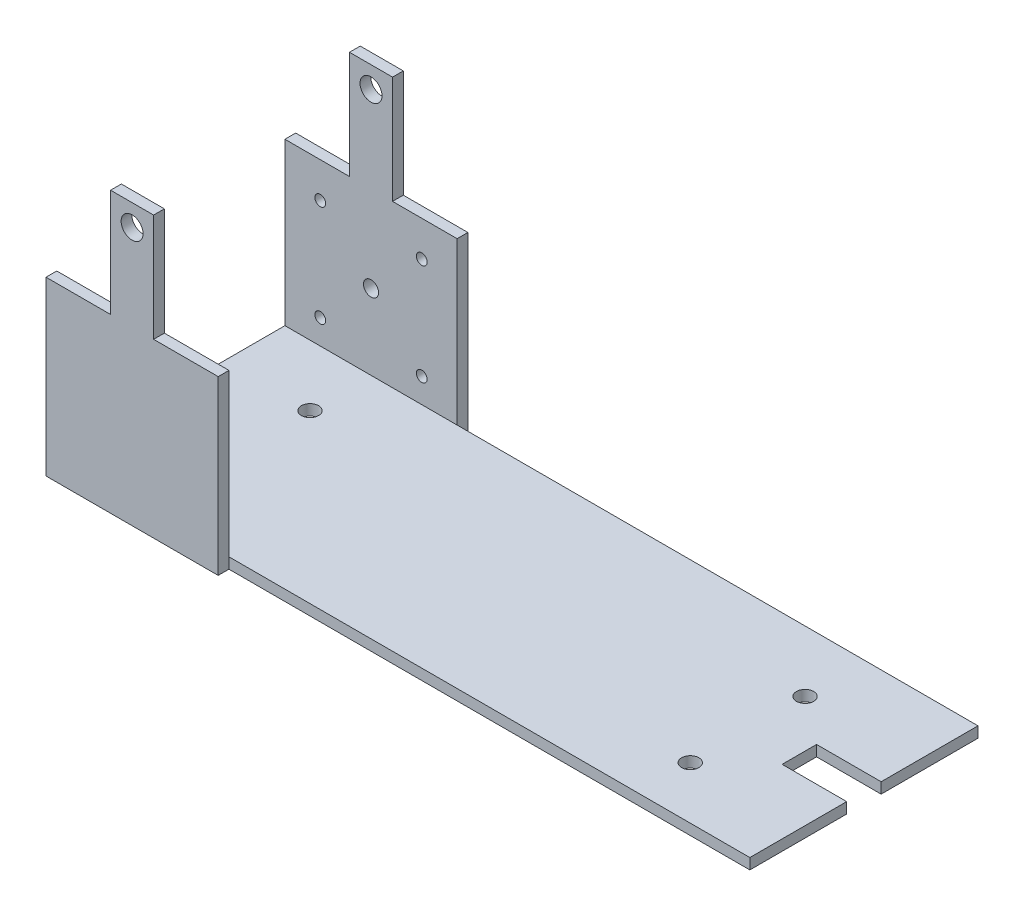
SolidWorks part; units mm, degrees
ref_plane "Front Plane" through (0, 0, 0) normal (0, 0, 1) x (1, 0, 0)
ref_plane "Top Plane" through (0, 0, 0) normal (0, 1, 0) x (1, 0, 0)
ref_plane "Right Plane" through (0, 0, 0) normal (1, 0, 0) x (0, 0, -1)
sketch "Sketch1" plane through (0, 0, 0) normal (0, 0, 1) x (1, 0, 0)
  line L0 (-40, -40) -> (-10, -40)
  line L2 (-10, -40) -> (-10, 10)
  line L3 (-10, 10) -> (10, 10)
  line L4 (10, -40) -> (10, 10)
  line L7 (40, -40) -> (40, -120)
  line L8 (40, -120) -> (-40, -120)
  line L9 (-40, -120) -> (-40, -40)
  line L10 (10, -40) -> (40, -40)
  circle A0 centre (0, 0) radius 5.1
  circle A1 centre (0, -80) radius 3.5
  dimension "D3" = 10.2
  dimension "D5" = 7
  dimension "D1" = 20
  dimension "D2" = 50
  dimension "D4" = 10
  dimension "D6" = 80
  dimension "D7" = 30
  dimension "D8" = 30
  dimension "D9" = 80
  dimension "D10" = 10
  dimension "D11" = 40
extrude "Boss-Extrude2" add sketch "Sketch1" along normal blind 5
sketch "Sketch2" plane through (0, 0, 5) normal (0, 0, 1) x (1, 0, 0)
  circle A0 centre (-23.57, -56.43) radius 2.5
  circle A1 centre (23.57, -56.43) radius 2.5
  circle A2 centre (-23.57, -103.57) radius 2.5
  circle A3 centre (23.57, -103.57) radius 2.5
extrude "Cut-Extrude1" cut sketch "Sketch2" against normal blind 10
sketch "Sketch3" plane through (0, 0, 5) normal (0, 0, 1) x (1, 0, 0)
  line L2 (-40, -120) -> (-40, -115)
  line L5 (-40, -115) -> (282, -115)
  line L6 (282, -115) -> (282, -120)
  line L7 (282, -120) -> (-40, -120)
  dimension "D1" = 5
  dimension "D2" = 322
extrude "Boss-Extrude3" add sketch "Sketch3" along normal blind 106
sketch "Sketch4" plane through (0, 0, 111) normal (0, 0, 1) x (1, 0, 0)
  line L0 (-40, -115) -> (-40, -120) construction
  line L1 (40, -115) -> (40, -40) construction
  line L2 (40, -40) -> (10, -40) construction
  line L3 (10, -40) -> (10, 10) construction
  line L4 (10, 10) -> (-10, 10) construction
  line L5 (-10, 10) -> (-10, -40) construction
  line L6 (-10, -40) -> (-40, -40) construction
  line L7 (-40, -40) -> (-40, -115) construction
  line L8 (-40, -115) -> (-40, -120)
  line L9 (40, -115) -> (40, -40)
  line L10 (40, -40) -> (10, -40)
  line L11 (10, -40) -> (10, 10)
  line L12 (10, 10) -> (-10, 10)
  line L13 (-10, 10) -> (-10, -40)
  line L14 (-10, -40) -> (-40, -40)
  line L15 (-40, -40) -> (-40, -115)
  line L20 (40, -115) -> (40, -120)
  line L21 (40, -120) -> (-40, -120)
  circle A0 centre (0, 0) radius 5.1 construction
  circle A1 centre (0, 0) radius 5.1
extrude "Boss-Extrude4" add sketch "Sketch4" along normal blind 5
sketch "Sketch5" plane through (0, -115, 0) normal (0, 1, 0) x (1, 0, 0)
  line L0 (282, -111) -> (282, -5) construction
  line L1 (282, -66) -> (252, -66)
  line L2 (282, -66) -> (282, -50)
  line L3 (282, -50) -> (252, -50)
  line L4 (252, -66) -> (252, -50)
  line L5 (282, -111) -> (40, -111) construction
  line L6 (282, -5) -> (40, -5) construction
  circle A0 centre (0, -33.3563) radius 4
  circle A1 centre (0, -86.6763) radius 4
  circle A2 centre (230, -86.6763) radius 4
  circle A3 centre (230, -33.3563) radius 4
  dimension "D4" = 8
  dimension "D5" = 8
  dimension "D6" = 8
  dimension "D7" = 8
  dimension "D1" = 45
  dimension "D2" = 45
  dimension "D3" = 30
  dimension "D8" = 230
extrude "Cut-Extrude2" cut sketch "Sketch5" against normal blind 10
